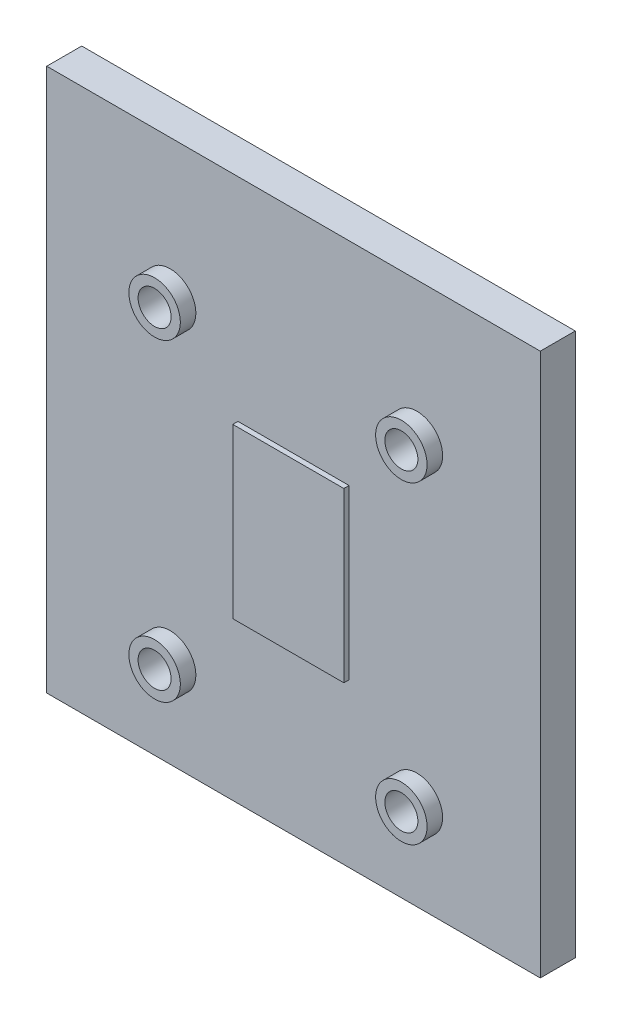
SolidWorks part; units mm, degrees
material "Сталь 08кп ГОСТ 535-88"
ref_plane "Спереди" through (0, 0, 0) normal (0, 0, 1) x (1, 0, 0)
ref_plane "Сверху" through (0, 0, 0) normal (0, 1, 0) x (1, 0, 0)
ref_plane "Справа" through (0, 0, 0) normal (1, 0, 0) x (0, 0, -1)
sketch "Sketch1" plane through (0, 0, 0) normal (0, 0, 1) x (1, 0, 0)
  line L0 (-25.4, -25.4) -> (25.4, -25.4)
  line L1 (25.4, -25.4) -> (25.4, 30.48)
  line L2 (25.4, 30.48) -> (-25.4, 30.48)
  line L3 (-25.4, 30.48) -> (-25.4, -25.4)
extrude "Boss-Extrude1" add sketch "Sketch1" against normal blind 3.6
sketch "Sketch2" plane through (0, 0, 0) normal (0, 0, 1) x (1, 0, 0)
  line L0 (-5.715, 8.6614) -> (5.715, 8.6614)
  line L1 (5.715, 8.6614) -> (5.715, -8.6614)
  line L2 (5.715, -8.6614) -> (-5.715, -8.6614)
  line L3 (-5.715, -8.6614) -> (-5.715, 8.6614)
extrude "Boss-Extrude2" add sketch "Sketch2" along normal blind 0.5332
ref_plane "Plane1" through (0, 16.129, 0) normal (0, -1, 0) x (1, 0, 0)
sketch "Sketch3" plane through (0, 16.129, 0) normal (0, -1, 0) x (1, 0, 0)
  line L0 (-10.052, 1.6) -> (-12.7, 1.6)
  line L1 (-12.7, 1.6) -> (-12.7, 0)
  line L2 (-12.7, 0) -> (-10.052, 0)
  line L3 (-10.052, 0) -> (-10.052, 1.6)
  line L4 (-12.7, 1.6) -> (-12.7, 0) construction
revolve "Revolve1" add sketch "Sketch3" angle 360 about L4
ref_plane "Plane2" through (0, -16.129, 0) normal (0, -1, 0) x (1, 0, 0)
sketch "Sketch4" plane through (0, -16.129, 0) normal (0, -1, 0) x (1, 0, 0)
  line L0 (-10.052, 1.6) -> (-12.7, 1.6)
  line L1 (-12.7, 1.6) -> (-12.7, 0)
  line L2 (-12.7, 0) -> (-10.052, 0)
  line L3 (-10.052, 0) -> (-10.052, 1.6)
  line L4 (-12.7, 1.6) -> (-12.7, 0) construction
revolve "Revolve2" add sketch "Sketch4" angle 360 about L4
sketch "Sketch5" plane through (0, -16.129, 0) normal (0, -1, 0) x (1, 0, 0)
  line L0 (15.348, 1.6) -> (12.7, 1.6)
  line L1 (12.7, 1.6) -> (12.7, 0)
  line L2 (12.7, 0) -> (15.348, 0)
  line L3 (15.348, 0) -> (15.348, 1.6)
  line L4 (12.7, 1.6) -> (12.7, 0) construction
revolve "Revolve3" add sketch "Sketch5" angle 360 about L4
sketch "Sketch6" plane through (0, 16.129, 0) normal (0, -1, 0) x (1, 0, 0)
  line L0 (15.348, 1.6) -> (12.7, 1.6)
  line L1 (12.7, 1.6) -> (12.7, 0)
  line L2 (12.7, 0) -> (15.348, 0)
  line L3 (15.348, 0) -> (15.348, 1.6)
  line L4 (12.7, 1.6) -> (12.7, 0) construction
revolve "Revolve4" add sketch "Sketch6" angle 360 about L4
hole_wizard "Ø3.4 (3.4) Diameter Hole1" positions "Sketch8" profile "Sketch7" hole size "Ø3.4" standard "ANSI Metric" end condition through all
sketch "Sketch8" plane through (0, 0, 1.6) normal (0, 0, 1) x (1, 0, 0)
  point P0 (-12.7, -16.129)
  point P1 (12.7, -16.129)
  point P2 (12.7, 16.129)
  point P3 (-12.7, 16.129)
sketch "Sketch7" plane through (-12.7, -16.129, 1.6) normal (1, 0, 0) x (0, -1, 0)
  line L0 (0, 0) -> (0, 5.2)
  line L1 (0, 5.2) -> (1.7, 5.2)
  line L2 (1.7, 5.2) -> (1.7, 0)
  line L5 (1.7, 0) -> (0, 0)
  line L11 (0, -6.35) -> (0, 107.95) construction
  dimension "Thru Hole Dia." = 3.4
  dimension "Thru Hole Depth" = 5.2
